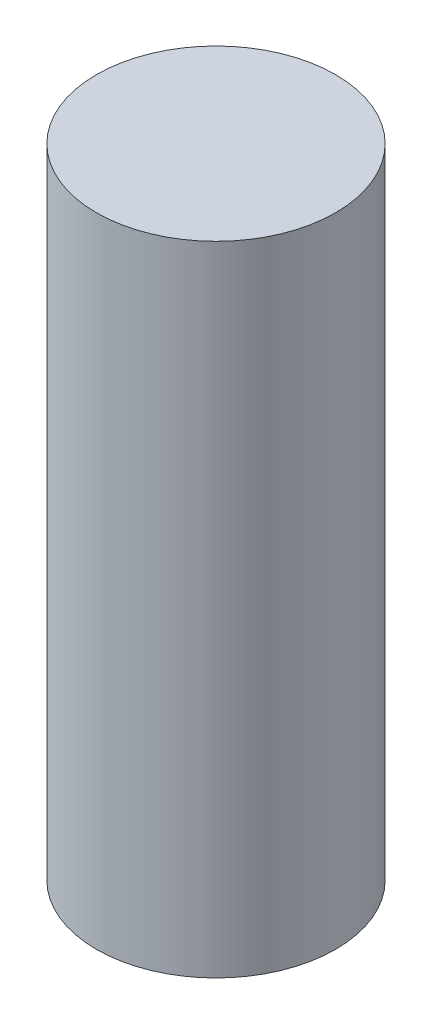
SolidWorks part; units mm, degrees
ref_plane "Front Plane" through (0, 0, 0) normal (0, 0, 1) x (1, 0, 0)
ref_plane "Top Plane" through (0, 0, 0) normal (0, 1, 0) x (1, 0, 0)
ref_plane "Right Plane" through (0, 0, 0) normal (1, 0, 0) x (0, 0, -1)
sketch "Sketch1" plane through (0, 0, 0) normal (0, 1, 0) x (1, 0, 0)
  circle A0 centre (0, 0) radius 15
extrude "Boss-Extrude1" add sketch "Sketch1" along normal blind 80
